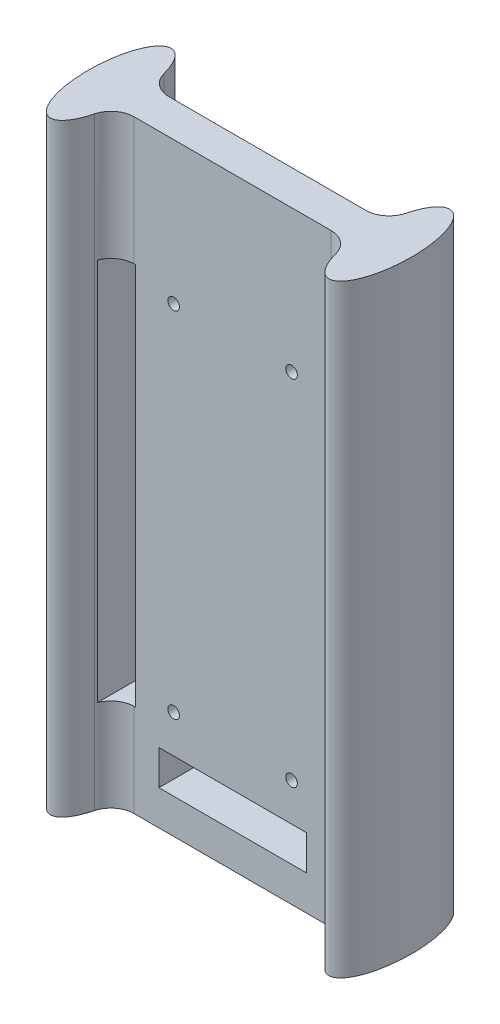
SolidWorks part; units mm, degrees
ref_plane "Front Plane" through (0, 0, 0) normal (0, 0, 1) x (1, 0, 0)
ref_plane "Top Plane" through (0, 0, 0) normal (0, 1, 0) x (1, 0, 0)
ref_plane "Right Plane" through (0, 0, 0) normal (1, 0, 0) x (0, 0, -1)
sketch "Sketch1" plane through (0, 0, 0) normal (0, 1, 0) x (1, 0, 0)
  line L0 (-30, 0) -> (-34.85, 0) construction
  line L1 (30, 3.75) -> (-30, 3.75)
  line L2 (30, 3.75) -> (30, -3.75)
  line L3 (30, -3.75) -> (-30, -3.75)
  line L4 (-30, 3.75) -> (-30, -3.75)
  line L5 (30, 3.75) -> (-30, -3.75) construction
  line L6 (30, -3.75) -> (-30, 3.75) construction
  line L7 (30, 0) -> (34.85, 0) construction
  ellipse E0 centre (-30, 0) end of major axis (-30, -13) minor radius 4.85
  ellipse E1 centre (30, 0) end of major axis (30, 13) minor radius 4.85
  point P0 (0, 0)
  dimension "D1" = 69.7
  dimension "D2" = 7.5
  dimension "D4" = 60
  dimension "D6" = 13
  dimension "D7" = 13
extrude "Boss-Extrude1" add sketch "Sketch1" along normal blind 130 contours E1 L1 E0 L3 | L3 E0 L1 L4 | L1 E0 L3 L4 | L1 E1 L3 L2 | L3 E1 L1 L2
fillet "Fillet1" radius 5 4 edges at (-25.3562, 65, -3.75) (25.3562, 65, -3.75) (25.3562, 65, 3.75) (-25.3562, 65, 3.75)
sketch "Sketch3" plane through (0, 0, -3.75) normal (0, 0, -1) x (-1, 0, 0)
  line L0 (0, 61.275) -> (0, 0) construction
  line L1 (15.875, 20) -> (-15.875, 20)
  line L2 (15.875, 20) -> (15.875, 102.55)
  line L3 (15.875, 102.55) -> (-15.875, 102.55)
  line L4 (-15.875, 20) -> (-15.875, 102.55)
  line L5 (15.875, 20) -> (-15.875, 102.55) construction
  line L6 (15.875, 102.55) -> (-15.875, 20) construction
  line L7 (21.1972, 0) -> (26.0334, 0) construction
  line L8 (-21.1972, 0) -> (21.1972, 0) construction
  line L9 (20.875, 102.55) -> (25.875, 102.55)
  line L10 (12.7, 23.175) -> (-12.7, 23.175)
  line L11 (12.7, 23.175) -> (12.7, 99.375)
  line L12 (12.7, 99.375) -> (-12.7, 99.375)
  line L13 (-12.7, 23.175) -> (-12.7, 99.375)
  line L14 (12.7, 23.175) -> (-12.7, 99.375) construction
  line L15 (12.7, 99.375) -> (-12.7, 23.175) construction
  line L16 (20.875, 102.55) -> (20.875, 20)
  line L17 (20.875, 20) -> (25.875, 20)
  line L18 (25.875, 102.55) -> (25.875, 20)
  line L20 (-15.875, 7.5) -> (15.875, 7.5)
  line L21 (-15.875, 7.5) -> (-15.875, 15)
  line L22 (-15.875, 15) -> (15.875, 15)
  line L23 (15.875, 7.5) -> (15.875, 15)
  point P0 (0, 61.275)
  point P18 (23.375, 20)
  dimension "D1" = 31.75
  dimension "D2" = 82.55
  dimension "D3" = 20
  dimension "D4" = 76.2
  dimension "D5" = 25.4
  dimension "D6" = 5
  dimension "D7" = 5
  dimension "D8" = 82.55
  dimension "D9" = 20
  dimension "D10" = 7.5
  dimension "D11" = 7.5
extrude "Cut-Extrude2" cut sketch "Sketch3" against normal through all both and the other way through all contours L21 L20 L23 L22 | L16 L9 L18 L17
hole_wizard "Tap Drill for M3x0.5 Tap1" positions "3DSketch1" profile "Sketch4" hole size "M3x0.5" standard "ANSI Metric" end condition through all
sketch3d "3DSketch1"
  point P0 (12.7, 99.375, -3.75)
  point P3 (-12.7, 99.375, -3.75)
  point P6 (-12.7, 23.175, -3.75)
  point P9 (12.7, 23.175, -3.75)
sketch "Sketch4" plane through (12.7, 99.375, -3.75) normal (1, 0, 0) x (0, 1, 0)
  line L0 (0, 0) -> (0, 16.75)
  line L1 (0, 16.75) -> (1.25, 16.75)
  line L2 (1.25, 16.75) -> (1.25, 0)
  line L5 (1.25, 0) -> (0, 0)
  line L11 (0, -6.35) -> (0, 107.95) construction
  dimension "Thru Hole Dia." = 2.5
  dimension "Thru Hole Depth" = 16.75
